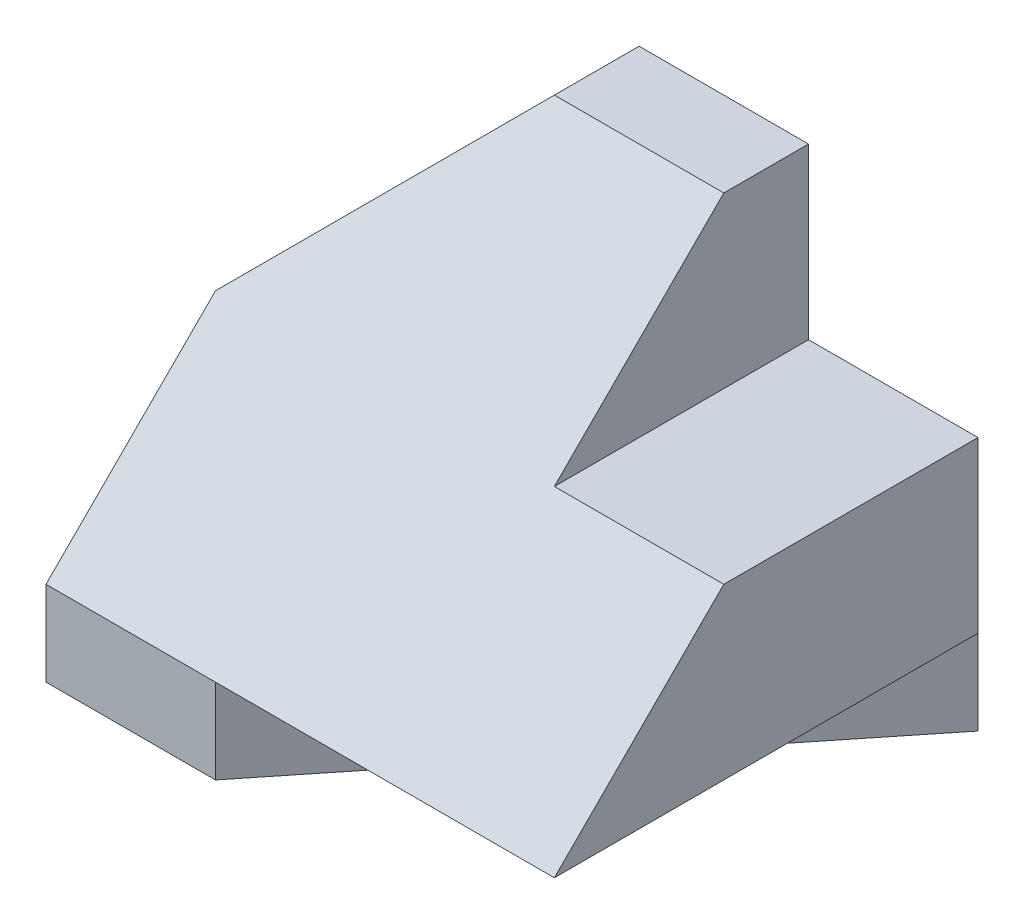
SolidWorks part; units mm, degrees
ref_plane "Front Plane" through (0, 0, 0) normal (0, 0, 1) x (1, 0, 0)
ref_plane "Top Plane" through (0, 0, 0) normal (0, 1, 0) x (1, 0, 0)
ref_plane "Right Plane" through (0, 0, 0) normal (1, 0, 0) x (0, 0, -1)
sketch "Sketch5" plane through (0, 0, 0) normal (0, 0, 1) x (1, 0, 0)
  line L1 (0, 0) -> (30, 0)
  line L2 (0, 0) -> (0, 25)
  line L3 (0, 25) -> (30, 25)
  line L4 (30, 0) -> (30, 25)
  dimension "D1" = 25
  dimension "D2" = 30
extrude "Boss-Extrude2" add sketch "Sketch5" along normal blind 25
sketch "Sketch6" plane through (0, 0, 0) normal (-1, 0, 0) x (0, 0, 1)
  line L0 (25, 25) -> (25, 5)
  line L1 (25, 25) -> (25, 0) construction
  line L2 (25, 5) -> (5, 25)
  line L3 (25, 25) -> (0, 25) construction
  line L4 (5, 25) -> (25, 25)
  dimension "D1" = 20
  dimension "D2" = 20
extrude "Cut-Extrude2" cut sketch "Sketch6" against normal blind 30
sketch "Sketch7" plane through (0, 0, 0) normal (-1, 0, 0) x (0, 0, 1)
  line L1 (0, 0) -> (5, 0)
  line L2 (0, 0) -> (0, 15)
  line L3 (0, 15) -> (5, 15)
  line L4 (5, 0) -> (5, 15)
  dimension "D1" = 5
  dimension "D2" = 15
extrude "Cut-Extrude3" cut sketch "Sketch7" against normal blind 10
sketch "Sketch9" plane through (0, 0, 0) normal (0, -1, 0) x (-1, 0, 0)
  line L0 (0, -25) -> (0, -5)
  line L1 (0, -5) -> (-10, -5)
  line L2 (-10, -5) -> (0, -25)
extrude "Cut-Extrude4" cut sketch "Sketch9" against normal blind 5
sketch "Sketch12" plane through (0, 25, 0) normal (0, 1, 0) x (1, 0, 0)
  line L1 (30, 0) -> (20, 0)
  line L2 (30, 0) -> (30, -10)
  line L3 (30, -10) -> (20, -10)
  line L4 (20, 0) -> (20, -10)
  dimension "D1" = 10
  dimension "D2" = 10
extrude "Cut-Extrude7" cut sketch "Sketch12" against normal blind 10
sketch "Sketch13" plane through (30, 0, 0) normal (1, 0, 0) x (0, 0, -1)
  line L0 (-10, 15) -> (-15, 15)
  line L1 (-10, 20) -> (-25, 5) construction
  line L2 (-15, 15) -> (-10, 20)
  line L3 (-10, 20) -> (-10, 15)
  dimension "D1" = 5
extrude "Cut-Extrude8" cut sketch "Sketch13" against normal blind 10
sketch "Sketch14" plane through (0, 0, 0) normal (0, 0, -1) x (-1, 0, 0)
  line L0 (0, 25) -> (-10, 25)
  line L1 (-20, 25) -> (0, 25) construction
  line L2 (-10, 25) -> (0, 15)
  line L3 (0, 15) -> (0, 25)
  dimension "D1" = 10
extrude "Cut-Extrude9" cut sketch "Sketch14" against normal blind 20
sketch "Sketch15" plane through (0, 0, 0) normal (0, -1, 0) x (-1, 0, 0)
  line L0 (-30, 0) -> (-30, -25)
  line L1 (-30, -25) -> (-10, -25)
  line L2 (0, -25) -> (-30, -25) construction
  line L3 (-10, -25) -> (-30, 0)
  dimension "D1" = 20
extrude "Cut-Extrude12" cut sketch "Sketch15" against normal blind 5
